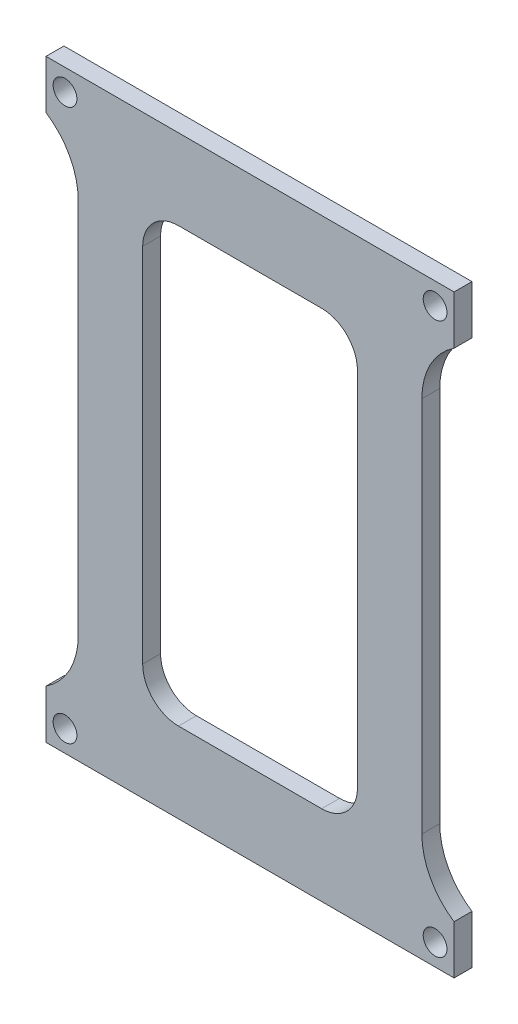
SolidWorks part; units mm, degrees
ref_plane "Plan de face" through (0, 0, 0) normal (0, 0, 1) x (1, 0, 0)
ref_plane "Plan de dessus" through (0, 0, 0) normal (0, 1, 0) x (1, 0, 0)
ref_plane "Plan de droite" through (0, 0, 0) normal (1, 0, 0) x (0, 0, -1)
sketch "Esquisse1" plane through (0, 0, 0) normal (0, 0, 1) x (1, 0, 0)
  line L101 (-29.7286, 42.1608) -> (-21.4286, 42.1608)
  line L187 (21.9714, 42.1608) -> (30.2714, 42.1608)
  line L188 (30.2714, 42.1608) -> (30.2714, 36.1608)
  line L189 (24.2714, 26.9956) -> (24.2714, -25.6741)
  line L190 (30.2714, -34.8392) -> (30.2714, -40.8392)
  line L191 (30.2714, -40.8392) -> (21.9714, -40.8392)
  line L195 (-21.4286, -40.8392) -> (-29.7286, -40.8392)
  line L196 (-29.7286, -40.8392) -> (-29.7286, -34.8392)
  line L197 (-23.7286, -25.6741) -> (-23.7286, 26.9956)
  line L198 (-29.7286, 42.1608) -> (-29.7286, 36.1608)
  line L199 (-21.4286, 42.1608) -> (21.9714, 42.1608)
  line L200 (-21.4286, -40.8392) -> (21.9714, -40.8392)
  line L203 (-14.7286, 30.9292) -> (15.2714, -29.6076) construction
  line L204 (-9.7286, 30.9292) -> (10.2714, 30.9292)
  line L205 (-14.7286, 25.9292) -> (-14.7286, -24.6076)
  line L206 (-9.7286, -29.6076) -> (10.2714, -29.6076)
  line L207 (15.2714, 25.9292) -> (15.2714, -24.6076)
  line L208 (15.2714, 30.9292) -> (-14.7286, -29.6076) construction
  line L209 (-29.7286, -40.8392) -> (30.2714, 42.1608) construction
  line L210 (30.2714, -40.8392) -> (-29.7286, 42.1608) construction
  arc A4 (30.2714, 36.1608) -> (24.2714, 26.9956) centre (34.2714, 26.9956) ccw
  arc A5 (24.2714, -25.6741) -> (30.2714, -34.8392) centre (34.2714, -25.6741) ccw
  arc A6 (-29.7286, -34.8392) -> (-23.7286, -25.6741) centre (-33.7286, -25.6741) ccw
  arc A7 (-23.7286, 26.9956) -> (-29.7286, 36.1608) centre (-33.7286, 26.9956) ccw
  circle A8 centre (-25.5786, 39.1608) radius 1.66
  circle A9 centre (26.1214, 39.1608) radius 1.66
  circle A10 centre (-25.5786, -37.8392) radius 1.66
  circle A11 centre (26.1214, -37.8392) radius 1.66
  arc A12 (-9.7286, -29.6076) -> (-14.7286, -24.6076) centre (-9.7286, -24.6076) cw
  arc A13 (15.2714, -24.6076) -> (10.2714, -29.6076) centre (10.2714, -24.6076) cw
  arc A14 (10.2714, 30.9292) -> (15.2714, 25.9292) centre (10.2714, 25.9292) cw
  arc A15 (-14.7286, 25.9292) -> (-9.7286, 30.9292) centre (-9.7286, 25.9292) cw
  point P32 (0.2714, 0.6608)
  point P33 (0.2714, 0.6608)
  point P34 (-41.6795, 3.2032)
  dimension "D2" = 5
  dimension "D1" = 30
extrude "Boss.-Extru.1" add sketch "Esquisse1" along normal blind 2.5
sketch "Esquisse2" plane through (0, 0, 0) normal (0, 0, -1) x (-1, 0, 0)
  line L0 (-30.2714, 36.1608) -> (-30.2714, 42.1608) construction
  line L1 (-41.907, 48.9155) -> (-28.7714, 48.9155)
  line L2 (-41.907, 48.9155) -> (-41.907, -48.3899)
  line L3 (-41.907, -48.3899) -> (-28.7714, -48.3899)
  line L4 (-28.7714, 48.9155) -> (-28.7714, -48.3899)
  line L5 (-30.2714, 42.1608) -> (29.7286, 42.1608) construction
  line L6 (-0.2714, 42.1608) -> (-0.2714, -40.8392) construction
  line L7 (29.7286, -40.8392) -> (-30.2714, -40.8392) construction
  line L8 (41.3642, -48.3899) -> (28.2286, -48.3899)
  line L9 (28.2286, 48.9155) -> (28.2286, -48.3899)
  line L10 (41.3642, 48.9155) -> (28.2286, 48.9155)
  line L11 (41.3642, 48.9155) -> (41.3642, -48.3899)
  dimension "D1" = 1.5
extrude "Enlèv. mat.-Extru.1" cut sketch "Esquisse2" against normal through all
